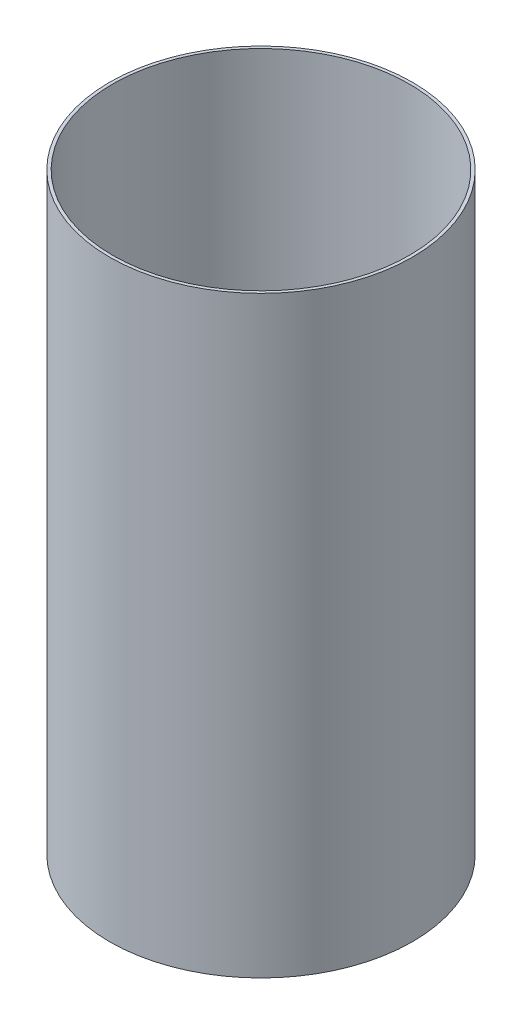
SolidWorks part; units mm, degrees
material "Hexcel AS4C (3000 Filaments)"
ref_plane "Front Plane" through (0, 0, 0) normal (0, 0, 1) x (1, 0, 0)
ref_plane "Top Plane" through (0, 0, 0) normal (0, 1, 0) x (1, 0, 0)
ref_plane "Right Plane" through (0, 0, 0) normal (1, 0, 0) x (0, 0, -1)
sketch "Sketch1" plane through (0, 0, 0) normal (0, 1, 0) x (1, 0, 0)
  circle A0 centre (0, 0) radius 76.2889
  circle A1 centre (0, 0) radius 77.8637
  dimension "D1" = 152.5778
  dimension "D2" = 155.7274
extrude "Boss-Extrude1" add sketch "Sketch1" along normal blind 304.8
